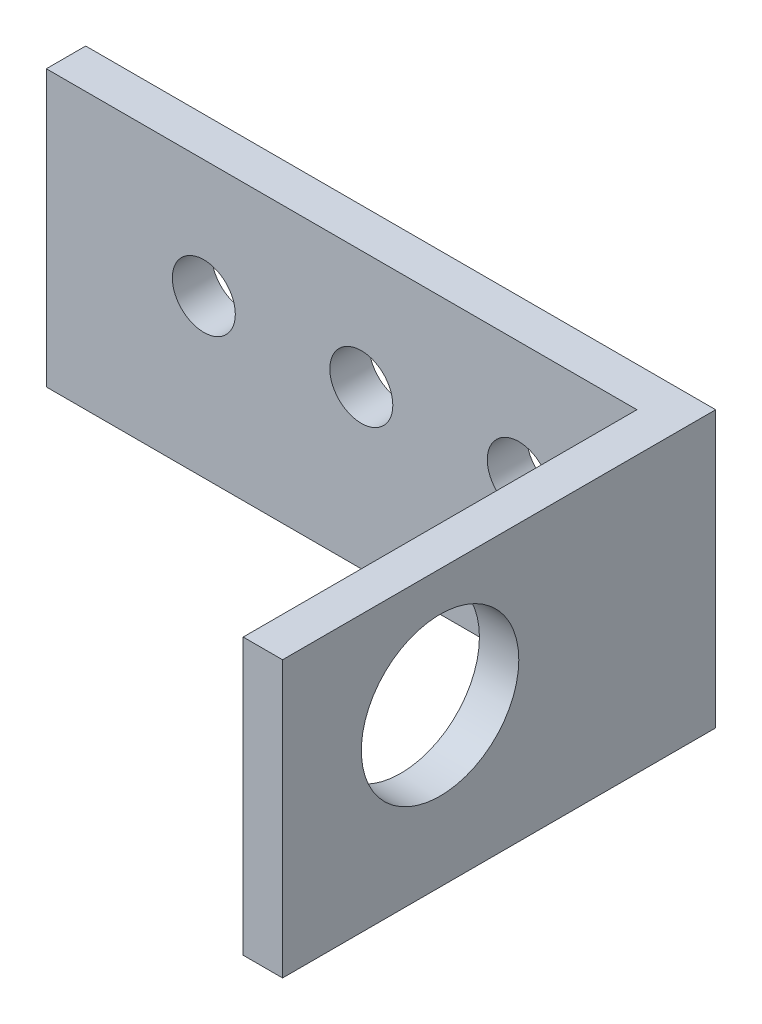
SolidWorks part; units mm, degrees
material "6061-T6 (SS)"
ref_plane "Front Plane" through (0, 0, 0) normal (0, 0, 1) x (1, 0, 0)
ref_plane "Top Plane" through (0, 0, 0) normal (0, 1, 0) x (1, 0, 0)
ref_plane "Right Plane" through (0, 0, 0) normal (1, 0, 0) x (0, 0, -1)
sketch "Sketch1" plane through (0, 0, 0) normal (0, 1, 0) x (1, 0, 0)
  line L1 (-25.4, -17.4625) -> (25.4, -17.4625)
  line L2 (-25.4, -17.4625) -> (-25.4, 17.4625)
  line L3 (-25.4, 17.4625) -> (25.4, 17.4625)
  line L4 (25.4, -17.4625) -> (25.4, 17.4625)
  line L5 (-25.4, -17.4625) -> (25.4, 17.4625) construction
  line L6 (-25.4, 17.4625) -> (25.4, -17.4625) construction
  line L7 (-25.4, -17.4625) -> (22.225, -17.4625)
  line L8 (-25.4, -17.4625) -> (-25.4, 14.2875)
  line L9 (-25.4, 14.2875) -> (22.225, 14.2875)
  line L10 (22.225, -17.4625) -> (22.225, 14.2875)
  point P0 (0, 0)
  dimension "D1" = 50.8
  dimension "D2" = 34.925
  dimension "D3" = 47.625
  dimension "D4" = 31.75
extrude "Boss-Extrude1" add sketch "Sketch1" along normal blind 22.225 contours L10 L1 L4 L3 L2 L9
sketch "Sketch2" plane through (25.4, 0, 0) normal (1, 0, 0) x (0, 0, -1)
  line L1 (-17.4625, 22.225) -> (-17.4625, 0) construction
  line L2 (-17.4625, 0) -> (17.4625, 0) construction
  circle A0 centre (-4.7625, 12.7) radius 6.35
  dimension "D1" = 12.7
  dimension "D2" = 12.7
  dimension "D3" = 12.7
extrude "Cut-Extrude1" cut sketch "Sketch2" against normal up to surface (3.175 mm away) up to face at (22.225, 11.1125, 1.5875)
sketch "Sketch3" plane through (0, 0, -14.2875) normal (0, 0, 1) x (1, 0, 0)
  line L0 (-25.4, 22.225) -> (-25.4, 0) construction
  line L1 (-25.4, 0) -> (22.225, 0) construction
  circle A0 centre (-12.7, 12.7) radius 2.54
  circle A1 centre (0, 12.7) radius 2.54
  circle A2 centre (12.7, 12.7) radius 2.54
  dimension "D1" = 5.08
  dimension "D2" = 12.7
  dimension "D3" = 12.7
  dimension "D4" = 12.7
  dimension "D5" = 12.7
extrude "Cut-Extrude2" cut sketch "Sketch3" against normal up to surface (3.175 mm away) up to face at (0, 11.1125, -17.4625)
